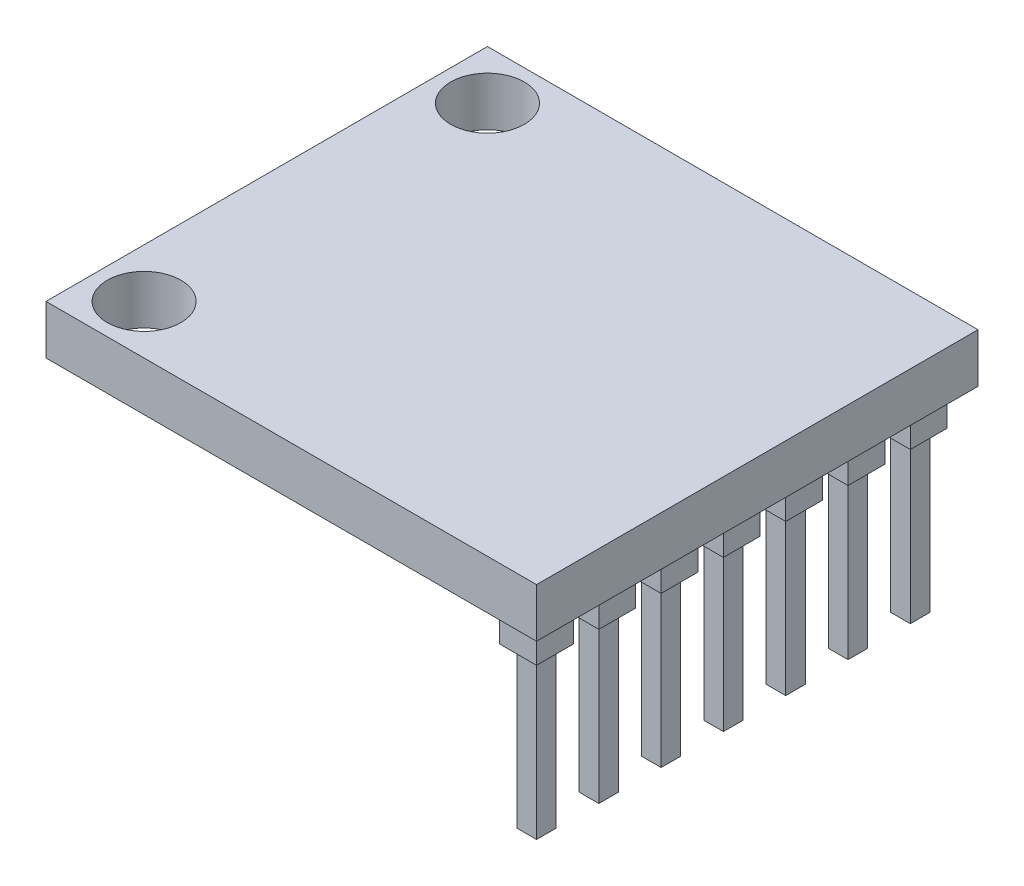
SolidWorks part; units mm, degrees
ref_plane "Ebene vorne" through (0, 0, 0) normal (0, 0, 1) x (1, 0, 0)
ref_plane "Ebene oben" through (0, 0, 0) normal (0, 1, 0) x (1, 0, 0)
ref_plane "Ebene rechts" through (0, 0, 0) normal (1, 0, 0) x (0, 0, -1)
sketch "Skizze1" plane through (0, 0, 0) normal (0, 1, 0) x (1, 0, 0)
  line L1 (-10, 9) -> (10, 9)
  line L2 (-10, 9) -> (-10, -9)
  line L3 (-10, -9) -> (10, -9)
  line L4 (10, 9) -> (10, -9)
  circle A0 centre (-8, -7) radius 1.5
  circle A1 centre (-8, 7) radius 1.5
  point P4 (10, 0)
  point P6 (0, 9)
  point P11 (0, 0)
  point P12 (0, 0)
  dimension "D3" = 3
  dimension "D4" = 3
  dimension "D5" = 0.5
  dimension "D6" = 0.5
  dimension "D7" = 0.5
  dimension "D1" = 18
  dimension "D2" = 20
extrude "Aufsatz-Linear austragen1" add sketch "Skizze1" along normal blind 2
sketch "Skizze2" plane through (0, 0, 0) normal (0, -1, 0) x (1, 0, 0)
  line L0 (10, 9) -> (10, -9) construction
  line L1 (9, 8) -> (8.2, 8)
  line L2 (9, 8) -> (9, 7.2)
  line L3 (9, 7.2) -> (8.2, 7.2)
  line L4 (8.2, 8) -> (8.2, 7.2)
  line L5 (-10, 9) -> (10, 9) construction
  dimension "D1" = 0.8
  dimension "D2" = 0.8
  dimension "D3" = 1
  dimension "D4" = 1
extrude "Aufsatz-Linear austragen2" add sketch "Skizze2" along normal blind 8
sketch "Skizze3" plane through (0, 0, 0) normal (0, -1, 0) x (-1, 0, 0)
  line L0 (-9, -8) -> (-8.2, -8) construction
  line L1 (-9.35, -8.35) -> (-7.85, -8.35)
  line L2 (-9.35, -8.35) -> (-9.35, -6.85)
  line L3 (-9.35, -6.85) -> (-7.85, -6.85)
  line L4 (-7.85, -8.35) -> (-7.85, -6.85)
  line L5 (-9, -7.2) -> (-9, -8) construction
  line L6 (-8.2, -8) -> (-8.2, -7.2) construction
  point P8 (-8.6, -8)
  point P9 (-8.6, -8.35)
  point P10 (-7.85, -7.6)
  point P13 (-8.2, -7.6)
  dimension "D1" = 1.5
  dimension "D2" = 1.5
extrude "Aufsatz-Linear austragen3" add sketch "Skizze3" along normal blind 1.5
pattern_linear "Lineares Muster1" count 7 spacing 2.54 along (0, 0, -1) of "Aufsatz-Linear austragen2", "Aufsatz-Linear austragen3"
